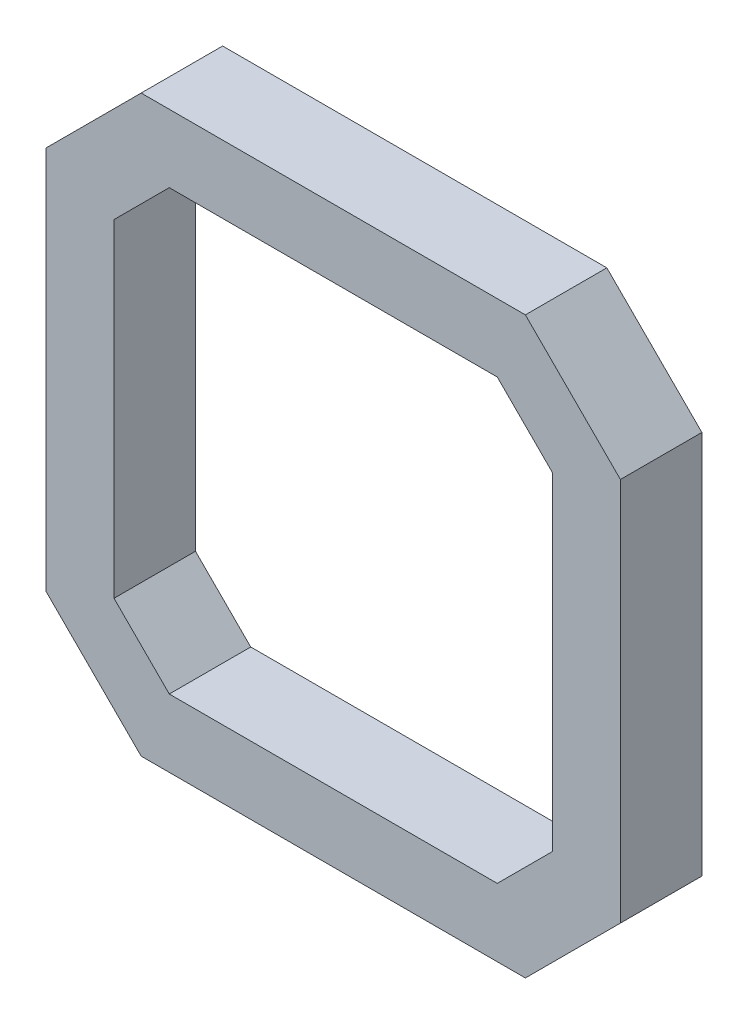
SolidWorks part; units mm, degrees
material "Ghisa grigia"
ref_plane "Piano frontale" through (0, 0, 0) normal (0, 0, 1) x (1, 0, 0)
ref_plane "Piano superiore" through (0, 0, 0) normal (0, 1, 0) x (1, 0, 0)
ref_plane "Piano destro" through (0, 0, 0) normal (1, 0, 0) x (0, 0, -1)
sketch "Schizzo1" plane through (0, 0, 0) normal (0, 0, 1) x (1, 0, 0)
  line L0 (-21.15, 14.15) -> (-14.15, 21.15)
  line L1 (-14.15, -21.15) -> (14.15, -21.15)
  line L2 (-21.15, -14.15) -> (-21.15, 14.15)
  line L3 (-14.15, 21.15) -> (14.15, 21.15)
  line L4 (21.15, -14.15) -> (21.15, 14.15)
  line L5 (-21.15, -21.15) -> (21.15, 21.15) construction
  line L6 (-21.15, 21.15) -> (21.15, -21.15) construction
  line L7 (14.15, 21.15) -> (21.15, 14.15)
  line L8 (14.15, -21.15) -> (21.15, -14.15)
  line L9 (-21.15, -14.15) -> (-14.15, -21.15)
  line L10 (-12.0789, 16.15) -> (12.0789, 16.15)
  line L11 (12.0789, 16.15) -> (16.15, 12.0789)
  line L12 (16.15, -12.0789) -> (16.15, 12.0789)
  line L13 (12.0789, -16.15) -> (16.15, -12.0789)
  line L14 (-12.0789, -16.15) -> (12.0789, -16.15)
  line L15 (-16.15, -12.0789) -> (-12.0789, -16.15)
  line L16 (-16.15, -12.0789) -> (-16.15, 12.0789)
  line L17 (-16.15, 12.0789) -> (-12.0789, 16.15)
  point P0 (0, 0)
  dimension "D1" = 42.3
  dimension "D2" = 42.3
  dimension "D3" = 5
extrude "Estrusione-Estrusione1" add sketch "Schizzo1" along normal blind 6
